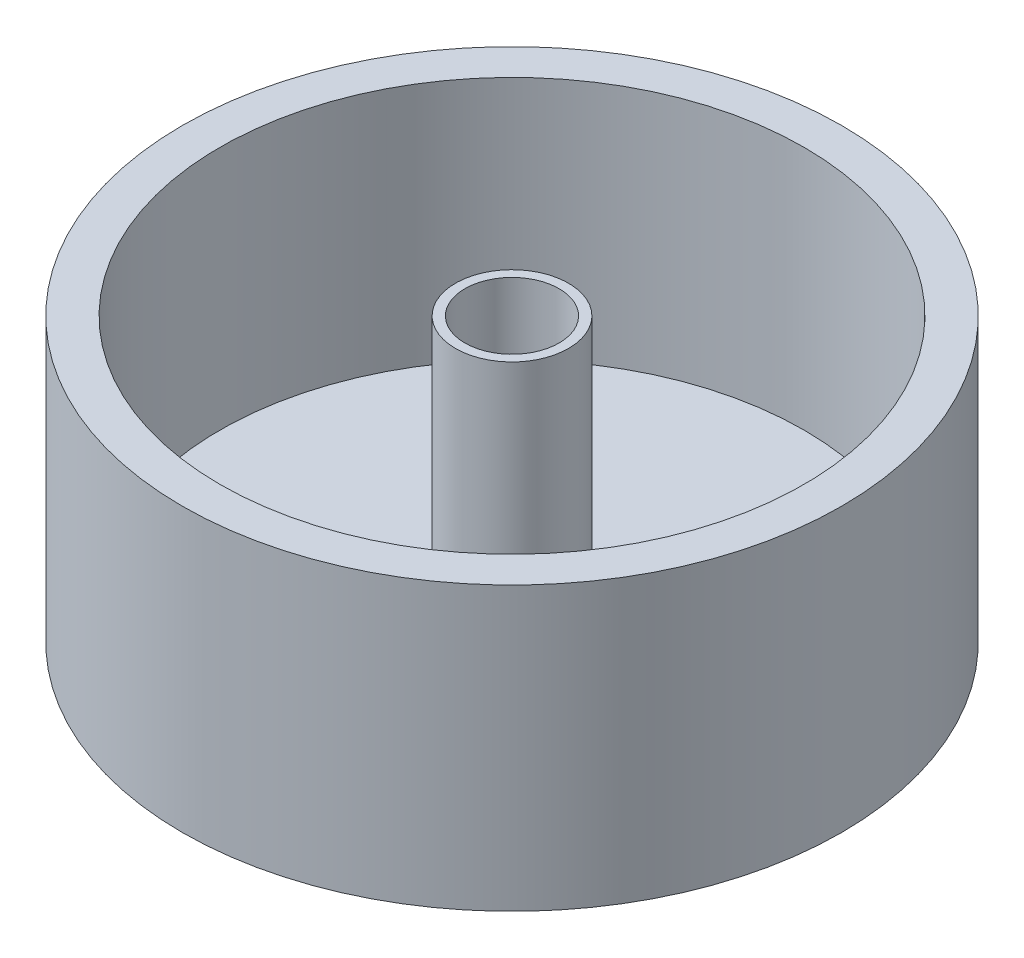
SolidWorks part; units mm, degrees
ref_plane "Plano frontal" through (0, 0, 0) normal (0, 0, 1) x (1, 0, 0)
ref_plane "Plano superior" through (0, 0, 0) normal (0, 1, 0) x (1, 0, 0)
ref_plane "Plano direito" through (0, 0, 0) normal (1, 0, 0) x (0, 0, -1)
sketch "Esboço1" plane through (0, 0, 0) normal (0, 1, 0) x (1, 0, 0)
  circle A0 centre (0, 0) radius 175
  dimension "D1" = 350
extrude "Ressalto-extrusão1" add sketch "Esboço1" along normal blind 20
sketch "Esboço3" plane through (0, 20, 0) normal (0, 1, 0) x (1, 0, 0)
  circle A0 centre (0, 0) radius 175
  circle A1 centre (0, 0) radius 155
  dimension "D1" = 310
extrude "Ressalto-extrusão3" add sketch "Esboço3" along normal blind 130
sketch "Esboço4" plane through (0, 20, 0) normal (0, 1, 0) x (1, 0, 0)
  circle A0 centre (0, 0) radius 25
  dimension "D1" = 50
extrude "Corte-extrusão1" cut sketch "Esboço4" against normal through all both and the other way through all
sketch "Esboço5" plane through (0, 20, 0) normal (0, 1, 0) x (1, 0, 0)
  circle A0 centre (0, 0) radius 25
  circle A1 centre (0, 0) radius 30
  dimension "D1" = 60
extrude "Ressalto-extrusão4" add sketch "Esboço5" along normal through all
